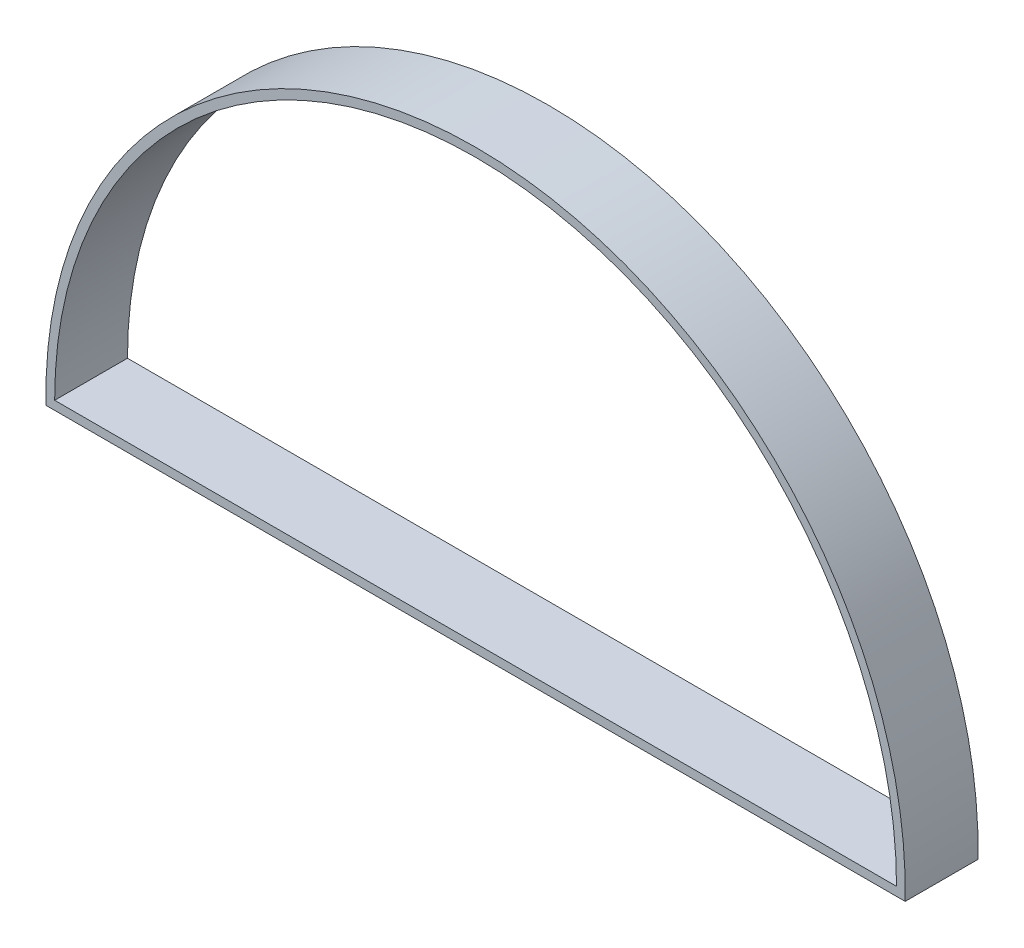
SolidWorks part; units mm, degrees
ref_plane "Plan de face" through (0, 0, 0) normal (0, 0, 1) x (1, 0, 0)
ref_plane "Plan de dessus" through (0, 0, 0) normal (0, 1, 0) x (1, 0, 0)
ref_plane "Plan de droite" through (0, 0, 0) normal (1, 0, 0) x (0, 0, -1)
sketch "Esquisse1" plane through (0, 0, 0) normal (0, 0, 1) x (1, 0, 0)
  line L0 (0, 0) -> (246, 0)
  line L1 (289, 0) -> (246, 0)
  arc A0 (0, 0) -> (289, 0) centre (144.5, 0) cw
  dimension "D1" = 289
extrude "Extru.-Mince1" add sketch "Esquisse1" along normal blind 25 thin
